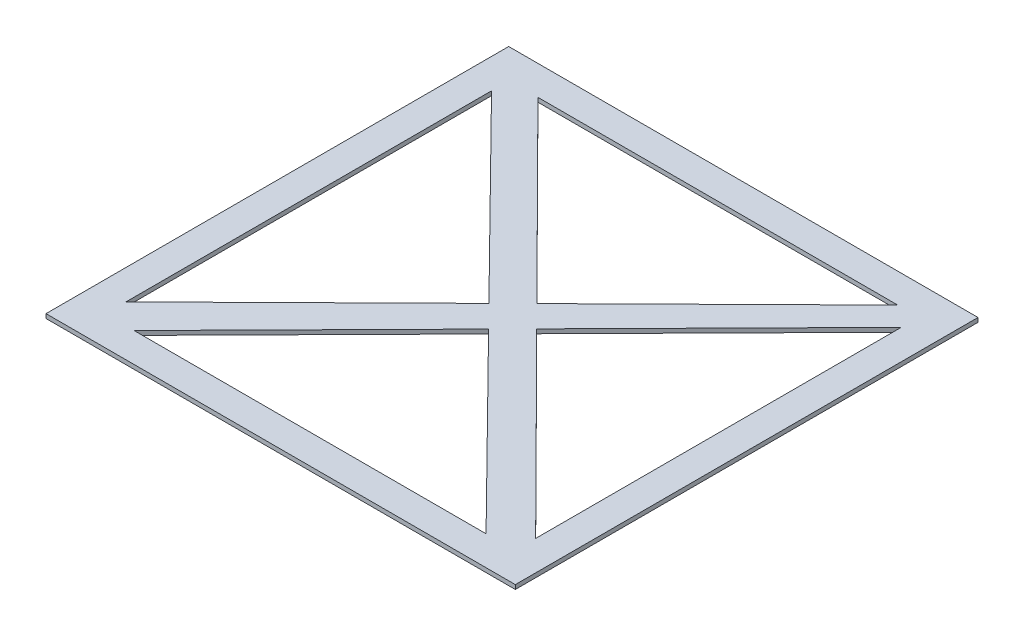
SolidWorks part; units mm, degrees
ref_plane "前视基准面" through (0, 0, 0) normal (0, 0, 1) x (1, 0, 0)
ref_plane "上视基准面" through (0, 0, 0) normal (0, 1, 0) x (1, 0, 0)
ref_plane "右视基准面" through (0, 0, 0) normal (1, 0, 0) x (0, 0, -1)
sketch "草图2" plane through (0, 0, 0) normal (0, 1, 0) x (1, 0, 0)
  line B0 (-1306.3467, 970.6864) -> (-1306.3467, -1207.9706)
  line B1 (-1306.3467, -1207.9706) -> (903.6188, -1207.9706)
  line B2 (903.6188, -1207.9706) -> (903.6188, 970.6864)
  line B3 (903.6188, 970.6864) -> (-1306.3467, 970.6864)
sketch_block_instance "块-Tingsquare-1"
sketch_block "块1"
sketch "草图3" plane through (0, 0, 0) normal (0, 1, 0) x (1, 0, 0)
  line L0 (-1306.3467, 970.6864) -> (903.6188, -1207.9706)
  line L1 (903.6188, 970.6864) -> (-1306.3467, -1207.9706)
  line L3 (-1230.5965, 896.0093) -> (827.8686, 896.0093)
  line L4 (-1230.5965, 896.0093) -> (-1230.5965, -1133.2935)
  line L5 (-1230.5965, -1133.2935) -> (827.8686, -1133.2935)
  line L6 (827.8686, 896.0093) -> (827.8686, -1133.2935)
  line L7 (-1230.5965, 896.0093) -> (827.8686, -1133.2935) construction
  line L8 (-1230.5965, -1133.2935) -> (827.8686, 896.0093) construction
  point P8 (-201.364, -118.6421)
sketch "草图4" plane through (0, 0, 0) normal (0, 1, 0) x (1, 0, 0)
  line L1 (-1030.1216, 832.2556) -> (664.0734, 832.2556)
  line L2 (-1165.9266, 749.5515) -> (-1165.9266, -971.8189)
  line L3 (-1030.1216, -1069.5398) -> (627.3937, -1069.5398)
  line L4 (763.1987, 749.5515) -> (763.1987, -971.8189)
  line L5 (-201.364, -228.8725) -> (627.3937, -1069.5398)
  line L6 (-191.5995, -11.295) -> (-1030.1216, 832.2556)
  line L7 (-1165.9266, 749.5515) -> (-305.329, -123.4134)
  line L8 (763.1987, 749.5515) -> (-88.8099, -114.701)
  line L9 (664.0734, 832.2556) -> (-191.5995, -11.295)
  line L10 (763.1987, -971.8189) -> (-88.8099, -114.701)
  line L11 (-305.329, -123.4134) -> (-1165.9266, -971.8189)
  line L12 (-201.364, -228.8725) -> (-1030.1216, -1069.5398)
  point P0 (-201.364, -118.6421)
sketch "草图5" plane through (0, 0, 0) normal (0, 1, 0) x (1, 0, 0)
  line L0 (-1306.3467, 970.6864) -> (-1306.3467, -1207.9706)
  line L1 (-1306.3467, -1207.9706) -> (903.6188, -1207.9706)
  line L2 (903.6188, -1207.9706) -> (903.6188, 970.6864)
  line L3 (903.6188, 970.6864) -> (-1306.3467, 970.6864)
  line L4 (-1165.9266, 749.5515) -> (-305.329, -123.4134)
  line L5 (-305.329, -123.4134) -> (-1165.9266, -971.8189)
  line L6 (-1165.9266, -971.8189) -> (-1165.9266, 749.5515)
  line L7 (-1030.1216, 832.2556) -> (664.0734, 832.2556)
  line L8 (664.0734, 832.2556) -> (-191.5995, -11.295)
  line L9 (-191.5995, -11.295) -> (-1030.1216, 832.2556)
  line L10 (-88.8099, -114.701) -> (763.1987, 749.5515)
  line L11 (763.1987, 749.5515) -> (763.1987, -971.8189)
  line L12 (763.1987, -971.8189) -> (-88.8099, -114.701)
  line L13 (-201.364, -228.8725) -> (-1030.1216, -1069.5398)
  line L14 (-1030.1216, -1069.5398) -> (627.3937, -1069.5398)
  line L15 (627.3937, -1069.5398) -> (-201.364, -228.8725)
extrude "凸台-拉伸1" add sketch "草图5" along normal blind 20
